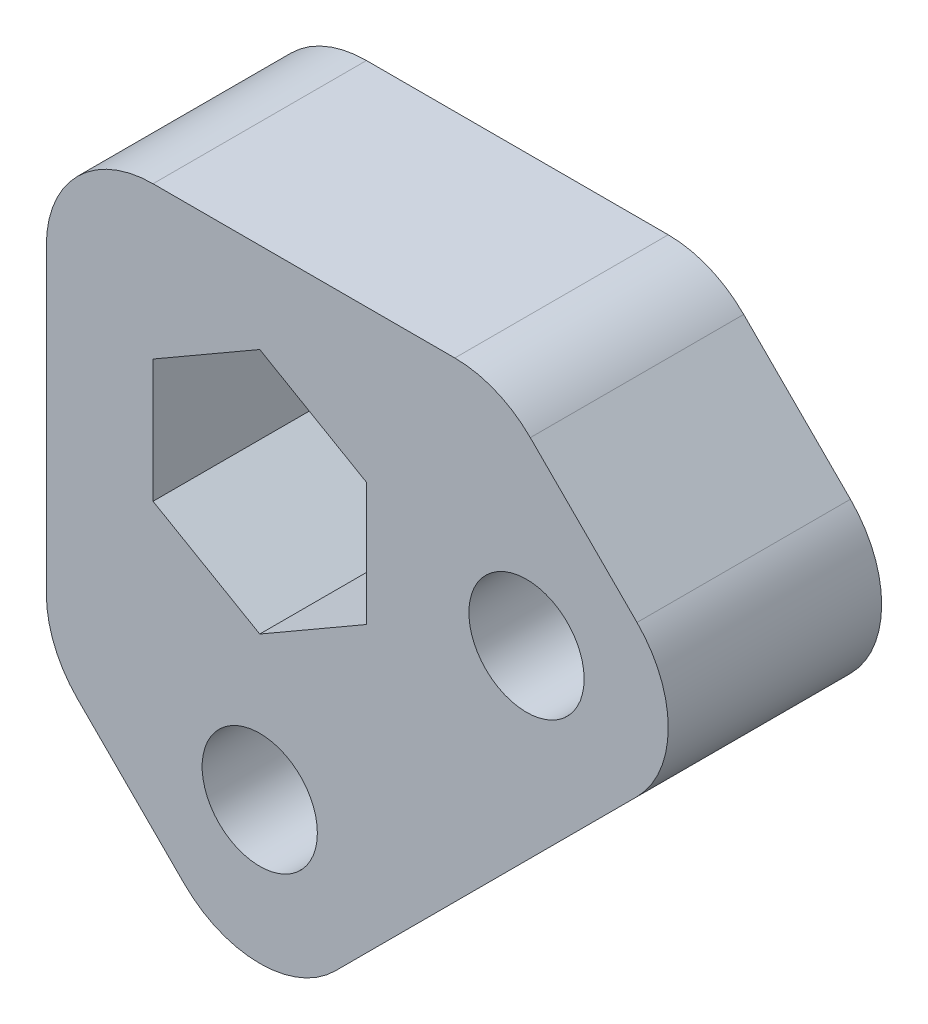
SolidWorks part; units mm, degrees
ref_plane "Front Plane" through (0, 0, 0) normal (0, 0, 1) x (1, 0, 0)
ref_plane "Top Plane" through (0, 0, 0) normal (0, 1, 0) x (1, 0, 0)
ref_plane "Right Plane" through (0, 0, 0) normal (1, 0, 0) x (0, 0, -1)
sketch "Sketch2" plane through (0, 0, 0) normal (0, 0, 1) x (1, 0, 0)
  line L0 (0, -55) -> (0, 55) construction
  line L1 (6.35, 3.6662) -> (0, 7.3323)
  line L2 (0, 7.3323) -> (-6.35, 3.6662)
  line L3 (-6.35, 3.6662) -> (-6.35, -3.6662)
  line L4 (-6.35, -3.6662) -> (0, -7.3323)
  line L5 (0, -7.3323) -> (6.35, -3.6662)
  line L6 (6.35, -3.6662) -> (6.35, 3.6662)
  line L9 (55, 0) -> (-55, 0) construction
  line L10 (-10.8401, -16.1006) -> (-4.4901, -22.4506)
  line L11 (4.4901, -22.4506) -> (22.4506, -4.4901)
  line L12 (22.4506, 4.4901) -> (16.1006, 10.8401)
  line L14 (-6.35, 12.7) -> (11.6105, 12.7)
  line L15 (-12.7, 6.35) -> (-12.7, -11.6105)
  line L16 (-15.875, 0) -> (26.9408, 0) construction
  line L17 (0, 12.446) -> (0, -26.9408) construction
  circle A0 centre (0, 0) radius 6.35 construction
  circle A2 centre (15.875, 0) radius 3.429
  circle A3 centre (0, -15.875) radius 3.429
  arc A6 (-9.525, 12.7) -> (9.525, 12.7) centre (0, 0) ccw construction
  arc A8 (-4.4901, -22.4506) -> (4.4901, -22.4506) centre (0, -17.9605) ccw
  arc A9 (22.4506, -4.4901) -> (22.4506, 4.4901) centre (17.9605, 0) ccw
  arc A12 (-12.7, -11.6105) -> (-10.8401, -16.1006) centre (-6.35, -11.6105) ccw
  arc A14 (-12.7, 6.35) -> (-6.35, 12.7) centre (-6.35, 6.35) cw
  arc A15 (11.6105, 12.7) -> (16.1006, 10.8401) centre (11.6105, 6.35) cw
  point P14 (0, 0)
  point P21 (0, 0)
  point P23 (0, 0)
  point P29 (0, 0)
  dimension "D1" = 12.7
  dimension "D3" = 12.7
  dimension "D4" = 12.7
  dimension "D6" = 38.1
  dimension "D7" = 6.35
  dimension "D2" = 31.75
  dimension "D8" = 6.858
  dimension "D9" = 6.35
  dimension "D10" = 6.35
  dimension "D5" = 19.05
extrude "Boss-Extrude1" add sketch "Sketch2" along normal blind 12.7
